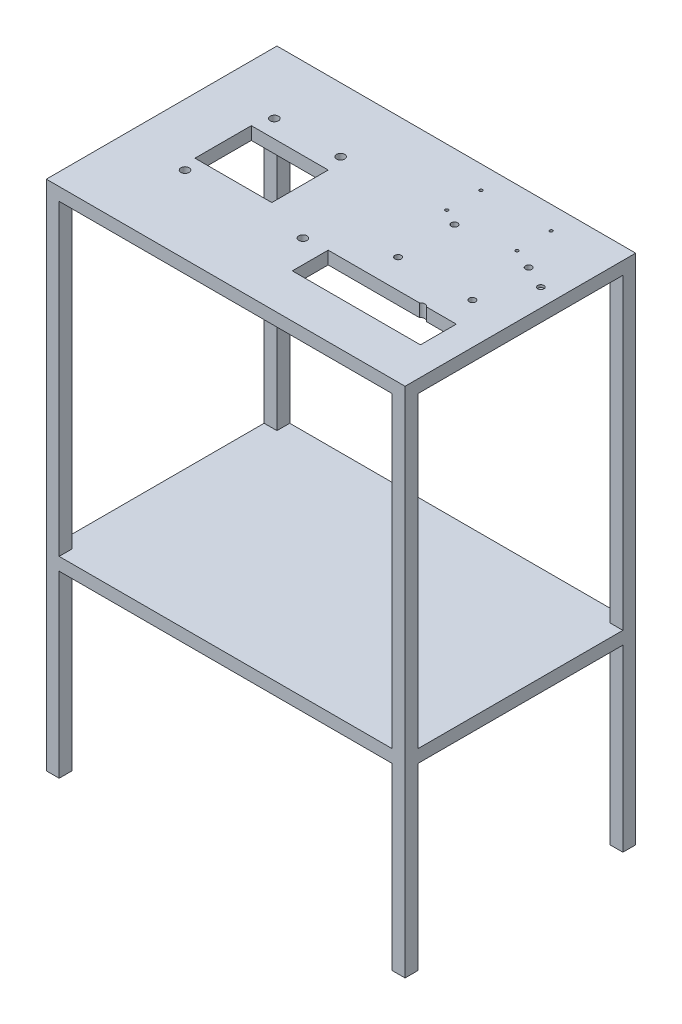
SolidWorks part; units mm, degrees
material "1023 Carbon Steel Sheet (SS)"
ref_plane "Front Plane" through (0, 0, 0) normal (0, 0, 1) x (1, 0, 0)
ref_plane "Top Plane" through (0, 0, 0) normal (0, 1, 0) x (1, 0, 0)
ref_plane "Right Plane" through (0, 0, 0) normal (1, 0, 0) x (0, 0, -1)
sketch "Sketch1" plane through (0, 0, 0) normal (0, 1, 0) x (1, 0, 0)
  line L1 (-350, 225) -> (350, 225)
  line L2 (-350, 225) -> (-350, -225)
  line L3 (-350, -225) -> (350, -225)
  line L4 (350, 225) -> (350, -225)
  line L5 (-350, 225) -> (350, -225) construction
  line L6 (-350, -225) -> (350, 225) construction
  point P0 (0, 0)
  dimension "D1" = 450
  dimension "D2" = 700
extrude "Boss-Extrude1" add sketch "Sketch1" along normal blind 1000
sketch "Sketch2" plane through (0, 0, 0) normal (0, 0, 1) x (1, 0, 0)
  line L0 (-350, 1000) -> (-350, 0) construction
  line L1 (-350, 1000) -> (350, 1000) construction
  line L2 (350, 1000) -> (350, 0) construction
  line L3 (-325, 975) -> (-325, 375)
  line L4 (-325, 975) -> (325, 975)
  line L5 (-325, 375) -> (325, 375)
  line L6 (325, 975) -> (325, 375)
  point P6 (350, 500)
  dimension "D2" = 600
  dimension "D3" = 25
  dimension "D4" = 25
  dimension "D5" = 25
extrude "Cut-Extrude1" cut sketch "Sketch2" against normal blind 250 and the other way blind 250
sketch "Sketch3" plane through (0, 0, 0) normal (0, 0, 1) x (1, 0, 0)
  line L0 (-350, 0) -> (350, 0) construction
  line L1 (-350, 1000) -> (-350, 0) construction
  line L2 (350, 1000) -> (350, 0) construction
  line L3 (325, 375) -> (-325, 375) construction
  line L5 (325, 350) -> (-325, 350)
  line L6 (325, 350) -> (325, 0)
  line L7 (325, 0) -> (-325, 0)
  line L8 (-325, 350) -> (-325, 0)
  dimension "D1" = 25
  dimension "D2" = 25
  dimension "D3" = 25
extrude "Cut-Extrude2" cut sketch "Sketch3" against normal blind 250 and the other way blind 250
sketch "Sketch4" plane through (0, 0, 0) normal (1, 0, 0) x (0, 0, -1)
  line L0 (225, 1000) -> (-225, 1000) construction
  line L1 (225, 1000) -> (225, 0) construction
  line L2 (-225, 1000) -> (-225, 0) construction
  line L3 (-200, 975) -> (-200, 375)
  line L4 (-200, 975) -> (200, 975)
  line L5 (200, 975) -> (200, 375)
  line L6 (200, 375) -> (-200, 375)
  dimension "D1" = 25
  dimension "D2" = 25
  dimension "D3" = 25
  dimension "D5" = 600
extrude "Cut-Extrude3" cut sketch "Sketch4" against normal blind 400 and the other way blind 400
sketch "Sketch5" plane through (0, 0, 0) normal (1, 0, 0) x (0, 0, -1)
  line L0 (-225, 0) -> (225, 0) construction
  line L1 (200, 375) -> (-200, 375) construction
  line L2 (-225, 1000) -> (-225, 0) construction
  line L3 (225, 1000) -> (225, 0) construction
  line L5 (200, 350) -> (-200, 350)
  line L6 (200, 350) -> (200, 0)
  line L7 (200, 0) -> (-200, 0)
  line L8 (-200, 350) -> (-200, 0)
  dimension "D1" = 25
  dimension "D2" = 25
  dimension "D3" = 25
extrude "Cut-Extrude4" cut sketch "Sketch5" against normal blind 400 and the other way blind 400
sketch "Esboço1" plane through (0, 1000, 0) normal (0, 1, 0) x (1, 0, 0)
  line L1 (-240.42, 65.42) -> (-90.42, 65.42)
  line L2 (-240.42, 65.42) -> (-240.42, -44.58)
  line L3 (-240.42, -44.58) -> (-90.42, -44.58)
  line L4 (-90.42, 65.42) -> (-90.42, -44.58)
  circle A0 centre (-100.84, 100) radius 8
  circle A1 centre (-230, 100) radius 8
  circle A2 centre (-230, -74.37) radius 8
  circle A3 centre (0, -74.37) radius 8
  circle A4 centre (230, -74.37) radius 8
  dimension "D1" = 16
  dimension "D2" = 16
  dimension "D3" = 16
  dimension "D4" = 16
  dimension "D5" = 16
extrude "Corte-extrusão1" cut sketch "Esboço1" against normal blind 50
sketch "Esboço2" plane through (0, 975, 0) normal (0, -1, 0) x (-1, 0, 0)
  line L1 (-295, -70) -> (-45, -70)
  line L2 (-295, -70) -> (-295, -140)
  line L3 (-295, -140) -> (-45, -140)
  line L4 (-45, -70) -> (-45, -140)
  line L5 (-295, -70) -> (-45, -140) construction
  line L6 (-295, -140) -> (-45, -70) construction
  line L7 (-325, -225) -> (325, -225) construction
  line L8 (-350, 200) -> (-350, -200) construction
  point P0 (-170, -105)
  dimension "D1" = 70
  dimension "D2" = 250
  dimension "D3" = 85
  dimension "D4" = 55
extrude "Corte-extrusão2" cut sketch "Esboço2" against normal through all
sketch "Esboço3" plane through (0, 1000, 0) normal (0, 1, 0) x (1, 0, 0)
  line L0 (350, -225) -> (350, 225) construction
  line L1 (350, 225) -> (-350, 225) construction
  line L2 (270, 96.3287) -> (270, -13.6713) construction
  line L3 (270, 96.3287) -> (125, 96.3287) construction
  line L4 (270, -13.6713) -> (125, -13.6713) construction
  line L5 (125, -13.6713) -> (125, 96.3287) construction
  circle A0 centre (270, -13.6713) radius 6.25
  circle A1 centre (270, 96.3287) radius 6.25
  circle A2 centre (125, 96.3287) radius 6.25
  circle A3 centre (125, -13.6713) radius 6.25
  dimension "D1" = 80
  dimension "D2" = 12.5
  dimension "D5" = 145
  dimension "D3" = 128.6713
  dimension "D4" = 110
extrude "Corte-extrusão3" cut sketch "Esboço3" against normal blind 10
sketch "Esboço5" plane through (0, 975, 0) normal (0, -1, 0) x (1, 0, 0)
  line L0 (350, -225) -> (-350, -225) construction
  line L1 (230, -180) -> (93, -180) construction
  line L2 (230, -180) -> (230, -113.3) construction
  line L3 (230, -113.3) -> (93, -113.3) construction
  line L4 (93, -180) -> (93, -113.3) construction
  line L5 (350, 225) -> (350, -225) construction
  circle A0 centre (93, -180) radius 3
  circle A1 centre (93, -113.3) radius 3
  circle A2 centre (230, -113.3) radius 3
  circle A3 centre (230, -180) radius 3
  dimension "D1" = 6
  dimension "D2" = 45
  dimension "D3" = 66.7
  dimension "D4" = 120
  dimension "D5" = 137
extrude "Corte-extrusão4" cut sketch "Esboço5" against normal through all
sketch "Esboço7" plane through (0, 1000, 0) normal (0, 1, 0) x (1, 0, 0)
  line L0 (350, -225) -> (350, 225) construction
  line L1 (350, 225) -> (-350, 225) construction
  circle A0 centre (315, 75) radius 6
  dimension "D1" = 12
  dimension "D2" = 35
  dimension "D3" = 150
extrude "Corte-extrusão5" cut sketch "Esboço7" against normal blind 5
